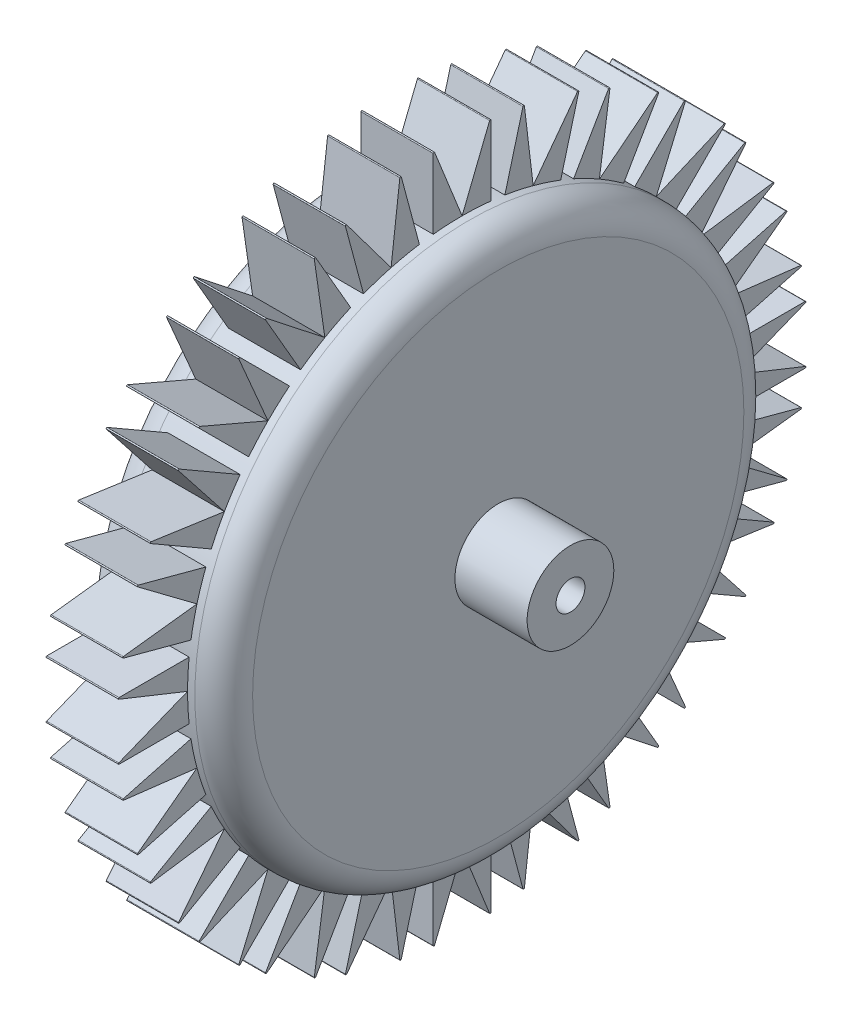
SolidWorks part; units mm, degrees
ref_plane "Front Plane" through (0, 0, 0) normal (0, 0, 1) x (1, 0, 0)
ref_plane "Top Plane" through (0, 0, 0) normal (0, 1, 0) x (1, 0, 0)
ref_plane "Right Plane" through (0, 0, 0) normal (1, 0, 0) x (0, 0, -1)
sketch "Sketch1" plane through (0, 0, 0) normal (1, 0, 0) x (0, 0, -1)
  circle A0 centre (0, 0) radius 19
  dimension "D1" = 38
extrude "Boss-Extrude1" add sketch "Sketch1" along normal blind 10
ref_plane "Plane1" through (5, 0, 0) normal (1, 0, 0) x (0, 0, -1)
sketch "Sketch2" plane through (5, 0, 0) normal (1, 0, 0) x (0, 0, -1)
  line L0 (0, 19) -> (2, 24)
  line L1 (2, 24) -> (-2, 24)
  line L2 (-2, 24) -> (0, 19)
  line L3 (0, 24) -> (0, 19) construction
  line L4 (2, 24) -> (2, 18.8944)
  line L5 (-2, 24) -> (-2, 18.8944)
  circle A0 centre (0, 0) radius 19
  dimension "D3" = 38
  dimension "D1" = 4
  dimension "D2" = 5
extrude "Boss-Extrude2" add sketch "Sketch2" along normal mid plane 5 contours A0 L2 L5 | A0 L4 L0
fillet "Fillet2" radius 0.05 2 edges at (5, 24, -2) (5, 24, 2)
pattern_circular "CirPattern1" count 24 every 15 about axis through (0, 0, 0) along (1, 0, 0) of "Boss-Extrude2", "Fillet2"
fillet "Fillet1" radius 2 2 edges at (0, 0, -19) (10, 0, -19)
sketch "Sketch3" plane through (0, 0, 0) normal (-1, 0, 0) x (0, 0, 1)
  line L0 (-12.6859, 4.8927) -> (7.3873, -11.4149)
  line L1 (7.3873, -11.4149) -> (13.139, 3.4983)
  line L2 (13.139, 3.4983) -> (0.733, 13.577)
  line L3 (0.733, 13.577) -> (-12.6859, 4.8927)
  line L4 (-12.6859, 4.8927) -> (-8.5734, -10.5531)
  line L5 (-8.5734, -10.5531) -> (7.3873, -11.4149)
  line L6 (-12.6859, 4.8927) -> (13.139, 3.4983)
  line L7 (13.139, 3.4983) -> (-8.5734, -10.5531)
  line L8 (-8.5734, -10.5531) -> (0.733, 13.577)
  line L9 (0.733, 13.577) -> (7.3873, -11.4149)
  circle A0 centre (0, 0) radius 11 construction
  dimension "D1" = 22
extrude "Boss-Extrude3" add sketch "Sketch3" along normal blind 0.5 contours L0 L8 L6 | L9 L6 L8 L0 L7 | L9 L8 L6 | L6 L9 L7 | L9 L7 L0 | L8 L7 L0
sketch "Sketch4" plane through (10, 0, 0) normal (1, 0, 0) x (0, 0, -1)
  circle A0 centre (0, 0) radius 1
  dimension "D1" = 2
extrude "Extrude-Thin1" add sketch "Sketch4" along normal blind 5 thin
